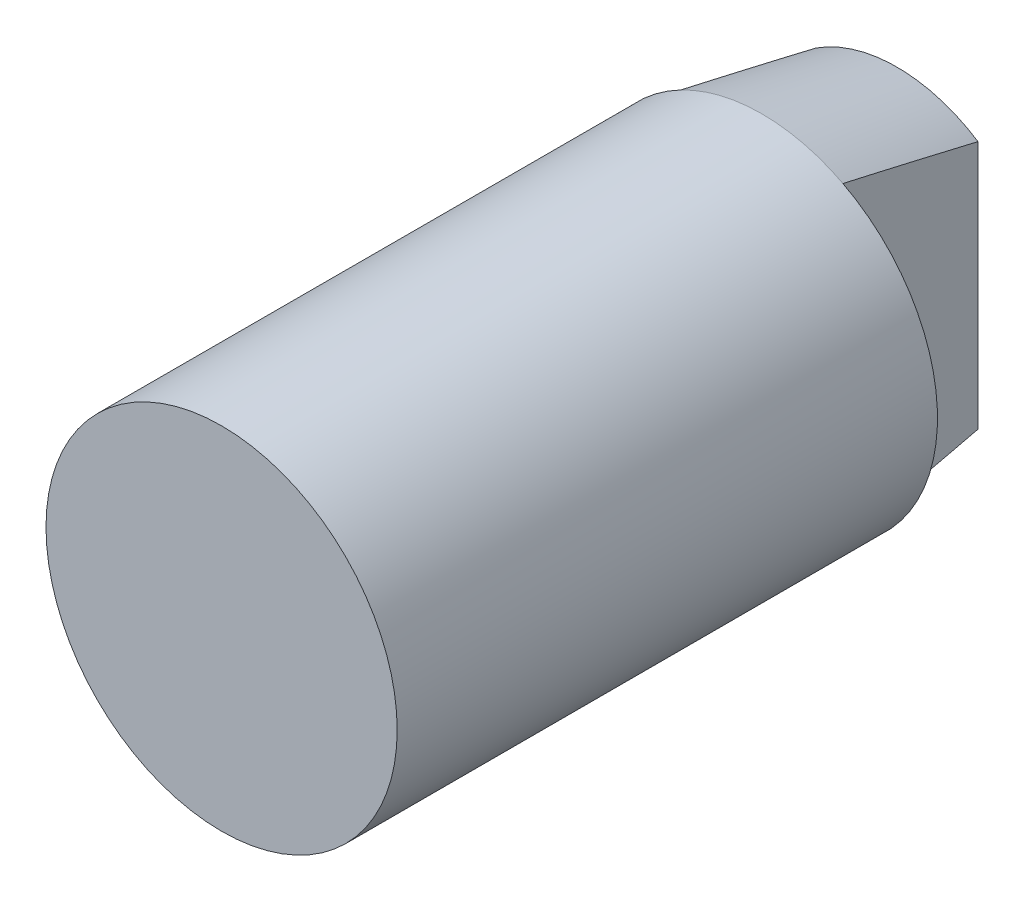
SolidWorks part; units mm, degrees
material "Plain Carbon Steel"
ref_plane "Front Plane" through (0, 0, 0) normal (0, 0, 1) x (1, 0, 0)
ref_plane "Top Plane" through (0, 0, 0) normal (0, 1, 0) x (1, 0, 0)
ref_plane "Right Plane" through (0, 0, 0) normal (1, 0, 0) x (0, 0, -1)
sketch "Sketch1" plane through (0, 0, 0) normal (1, 0, 0) x (0, 0, -1)
  line L0 (0, 0) -> (0, 6.5)
  line L1 (0, 6.5) -> (20, 6.5)
  line L2 (20, 6.5) -> (25, 5.5)
  line L3 (25, 5.5) -> (25, 0)
  line L4 (25, 0) -> (0, 0)
  dimension "D1" = 20
  dimension "D2" = 5.5
  dimension "D3" = 5
  dimension "D4" = 6.5
revolve "Revolve1" add sketch "Sketch1" angle 360 about L4
sketch "Sketch2" plane through (0, 0, -25) normal (0, 0, -1) x (-1, 0, 0)
  line L0 (-3, 5.7663) -> (-3, -5.7663)
  line L1 (3, 5.7663) -> (3, -5.7663)
  circle A2 centre (0, 0) radius 6.5 construction
  arc A3 (-3, 5.7663) -> (-3, -5.7663) centre (0, 0) ccw
  arc A4 (3, -5.7663) -> (3, 5.7663) centre (0, 0) ccw
  dimension "D1" = 6
extrude "Cut-Extrude1" cut sketch "Sketch2" against normal blind 5
sketch "Sketch3" plane through (0, 0, -20) normal (0, 0, -1) x (-1, 0, 0)
  line L1 (9.5, -2.5) -> (3.5, -2.5)
  line L2 (9.5, -2.5) -> (9.5, 2.5)
  line L3 (9.5, 2.5) -> (3.5, 2.5)
  line L4 (3.5, -2.5) -> (3.5, 2.5)
  line L5 (9.5, -2.5) -> (3.5, 2.5) construction
  line L6 (9.5, 2.5) -> (3.5, -2.5) construction
  arc A0 (3, -5.7663) -> (3, 5.7663) centre (0, 0) ccw construction
  point P0 (6.5, 0)
  dimension "D1" = 6
  dimension "D2" = 5
extrude "Cut-Extrude2" cut sketch "Sketch3" against normal blind 12
